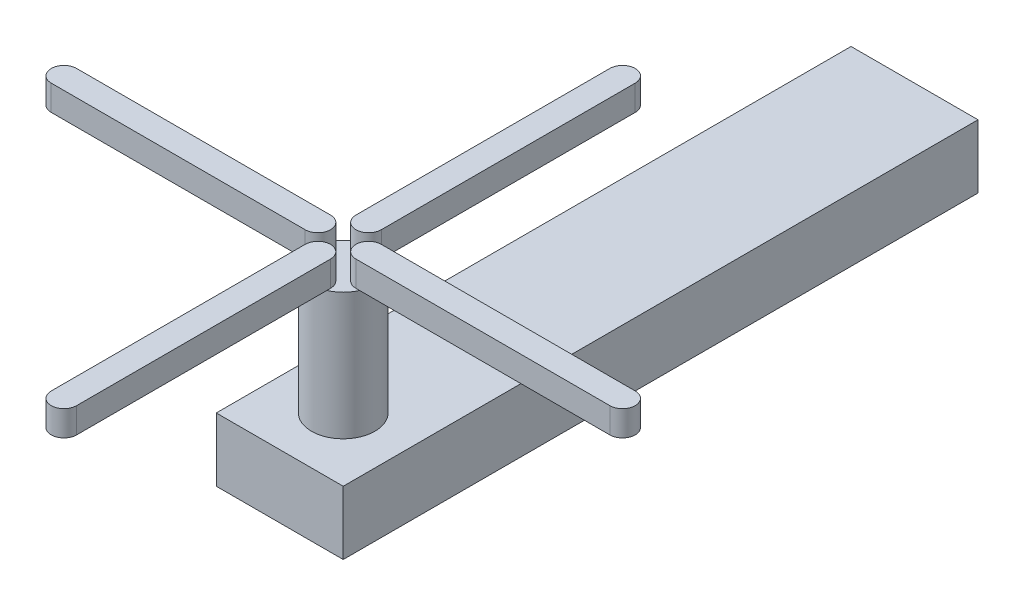
SolidWorks part; units mm, degrees
ref_plane "Front Plane" through (0, 0, 0) normal (0, 0, 1) x (1, 0, 0)
ref_plane "Top Plane" through (0, 0, 0) normal (0, 1, 0) x (1, 0, 0)
ref_plane "Right Plane" through (0, 0, 0) normal (1, 0, 0) x (0, 0, -1)
sketch "Sketch1" plane through (0, 0, 0) normal (0, 0, 1) x (1, 0, 0)
  line L1 (-12.7, 6.35) -> (12.7, 6.35)
  line L2 (-12.7, 6.35) -> (-12.7, -6.35)
  line L3 (-12.7, -6.35) -> (12.7, -6.35)
  line L4 (12.7, 6.35) -> (12.7, -6.35)
  point P4 (-12.7, 0)
  point P6 (0, 6.35)
  dimension "D1" = 12.7
  dimension "D2" = 25.4
extrude "Boss-Extrude1" add sketch "Sketch1" along normal blind 127
sketch "Sketch2" plane through (0, 6.35, 0) normal (0, 1, 0) x (1, 0, 0)
  line L0 (12.7, -127) -> (-12.7, -127) construction
  circle A0 centre (0, -114.3) radius 6.35
  dimension "D1" = 12.7
  dimension "D2" = 12.7
extrude "Boss-Extrude2" add sketch "Sketch2" along normal blind 25.4
sketch "Sketch3" plane through (0, 31.75, 0) normal (0, 1, 0) x (1, 0, 0)
  line L0 (5.08, -114.3) -> (55.88, -114.3) construction
  line L1 (5.08, -111.76) -> (55.88, -111.76)
  line L2 (5.08, -116.84) -> (55.88, -116.84)
  line L3 (-2.54, -119.38) -> (-2.54, -170.18)
  line L6 (2.54, -119.38) -> (2.54, -170.18)
  line L9 (0, -119.38) -> (0, -170.18) construction
  line L12 (-5.08, -111.76) -> (-55.88, -111.76)
  line L13 (-5.08, -116.84) -> (-55.88, -116.84)
  line L14 (-5.08, -114.3) -> (-55.88, -114.3) construction
  line L15 (2.54, -109.22) -> (2.54, -58.42)
  line L16 (-2.54, -109.22) -> (-2.54, -58.42)
  line L17 (0, -109.22) -> (0, -58.42) construction
  arc A0 (5.08, -111.76) -> (5.08, -116.84) centre (5.08, -114.3) ccw
  arc A1 (55.88, -116.84) -> (55.88, -111.76) centre (55.88, -114.3) ccw
  arc A8 (2.54, -119.38) -> (-2.54, -119.38) centre (0, -119.38) ccw
  arc A9 (-2.54, -170.18) -> (2.54, -170.18) centre (0, -170.18) ccw
  arc A10 (-5.08, -116.84) -> (-5.08, -111.76) centre (-5.08, -114.3) ccw
  arc A11 (-55.88, -111.76) -> (-55.88, -116.84) centre (-55.88, -114.3) ccw
  arc A12 (-2.54, -109.22) -> (2.54, -109.22) centre (0, -109.22) ccw
  arc A13 (2.54, -58.42) -> (-2.54, -58.42) centre (0, -58.42) ccw
  point P0 (0, -114.3)
  point P5 (30.48, -114.3)
  point P15 (0, -144.78)
  point P22 (-30.48, -114.3)
  point P29 (0, -83.82)
  point P34 (0, -114.3)
  dimension "D1" = 5.08
  dimension "D2" = 50.8
  dimension "D3" = 5.08
  dimension "D4" = 4
extrude "Boss-Extrude3" add sketch "Sketch3" along normal blind 5.08
